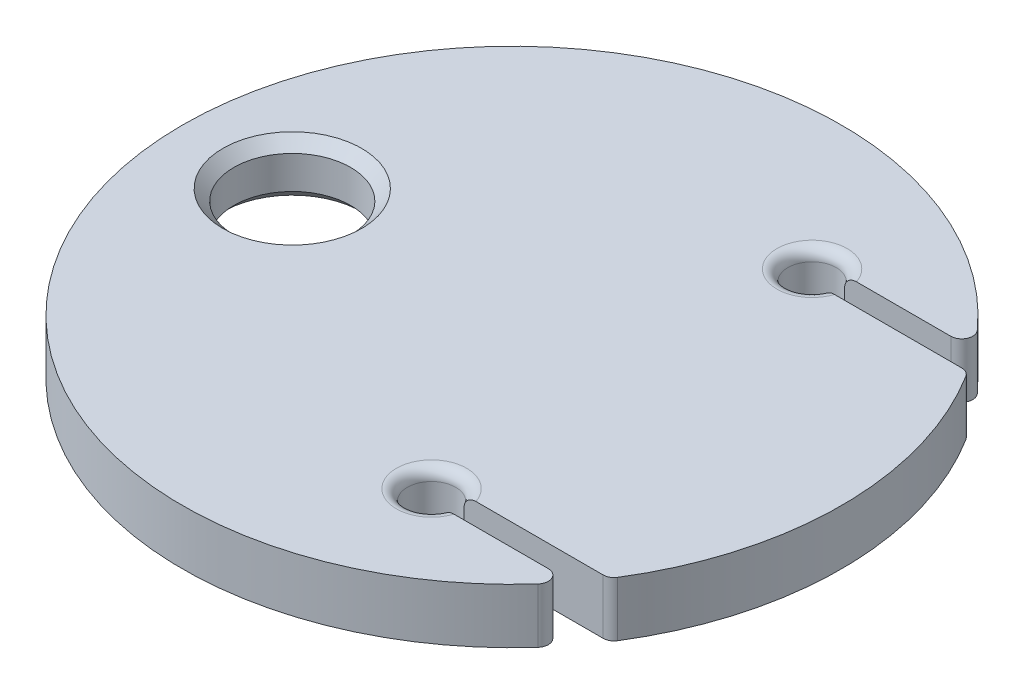
SolidWorks part; units mm, degrees
ref_plane "Front Plane" through (0, 0, 0) normal (0, 0, 1) x (1, 0, 0)
ref_plane "Top Plane" through (0, 0, 0) normal (0, 1, 0) x (1, 0, 0)
ref_plane "Right Plane" through (0, 0, 0) normal (1, 0, 0) x (0, 0, -1)
sketch "Sketch1" plane through (0, 0, 0) normal (0, 1, 0) x (1, 0, 0)
  circle A0 centre (0, 0) radius 19.05
  dimension "D1" = 38.1
extrude "Boss-Extrude1" add sketch "Sketch1" along normal blind 3.175
sketch "Sketch2" plane through (0, 3.175, 0) normal (0, 1, 0) x (1, 0, 0)
  line L0 (6.35, -10.9985) -> (6.35, 10.9985) construction
  line L1 (6.35, 10.9985) -> (-6.35, 10.9985) construction
  line L2 (6.35, -10.9985) -> (-6.35, -10.9985) construction
  line L3 (10.0041, -7.8235) -> (-10.0041, -7.8235) construction
  line L4 (10.0041, 7.8235) -> (-10.0041, 7.8235) construction
  line L5 (10.0041, -7.8235) -> (10.0041, 7.8235) construction
  circle A0 centre (0, 0) radius 12.7 construction
  point P6 (6.35, 0)
  dimension "D1" = 25.4
  dimension "D2" = 6.35
  dimension "D3" = 3.175
hole_wizard "Tiedown Hole" positions "Sketch3" profile "Sketch4" hole size "1/4" standard "ANSI Inch" end condition through all
sketch "Sketch3" plane through (0, 3.175, 0) normal (0, 1, 0) x (1, 0, 0)
  circle A0 centre (0, 0) radius 12.7 construction
  circle A1 centre (0, 0) radius 12.7 construction
  point P4 (-12.7, 0)
sketch "Sketch4" plane through (-12.7, 3.175, 0) normal (1, 0, 0) x (0, 0, 1)
  line L0 (0, 0) -> (0, 3.175)
  line L1 (0, 3.175) -> (3.3782, 3.175)
  line L2 (3.3782, 3.175) -> (3.3782, 0)
  line L5 (3.3782, 0) -> (0, 0)
  line L11 (0, -6.35) -> (0, 107.95) construction
  dimension "Thru Hole Dia." = 6.7564
  dimension "Thru Hole Depth" = 3.175
sketch3d "3DSketch1"
  line L0 (6.35, 3.175, 10.9985) -> (6.35, 3.175, 22.6356) construction
  line L1 (6.35, 3.175, 10.9985) -> (6.35, 3.175, -10.9985) construction
  line L2 (6.35, 3.175, -10.9985) -> (6.35, 3.175, -21.5348) construction
  line L3 (6.35, 3.175, -7.8235) -> (6.35, 3.175, -19.0222) construction
  line L4 (6.35, 3.175, 7.8235) -> (6.35, 3.175, 19.2587) construction
  dimension "D1" = 180
  dimension "D2" = 180
  dimension "D3" = 3.175
  dimension "D4" = 3.175
ref_plane "Plane1" through (0, 3.175, 0) normal (0, 1, 0) x (1, 0, 0)
ref_plane "Plane2" through (0, 3.175, 0) normal (0, -1, 0) x (-1, 0, 0)
hole_wizard "Monofilament Hole" positions "Sketch6" profile "Sketch7" hole size "#35" standard "ANSI Inch" end condition through all
sketch "Sketch6" plane through (0, 3.175, 0) normal (0, -1, 0) x (-1, 0, 0)
  point P0 (-6.35, 10.9985)
sketch "Sketch7" plane through (6.35, 3.175, -10.9985) normal (1, 0, 0) x (0, 0, 1)
  line L0 (0, 0) -> (0, 3.175)
  line L1 (0, 3.175) -> (1.397, 3.175)
  line L2 (1.397, 3.175) -> (1.397, 0)
  line L5 (1.397, 0) -> (0, 0)
  line L11 (0, -6.35) -> (0, 107.95) construction
  dimension "Thru Hole Dia." = 2.794
  dimension "Thru Hole Depth" = 3.175
hole_wizard "Monofilament Hole 2" positions "Sketch8" profile "Sketch9" hole size "#35" standard "ANSI Inch" end condition through all
sketch "Sketch8" plane through (0, 3.175, 0) normal (0, 1, 0) x (1, 0, 0)
  point P3 (6.35, -10.9985)
sketch "Sketch9" plane through (6.35, 3.175, 10.9985) normal (1, 0, 0) x (0, 0, 1)
  line L0 (0, 0) -> (0, 3.175)
  line L1 (0, 3.175) -> (1.397, 3.175)
  line L2 (1.397, 3.175) -> (1.397, 0)
  line L5 (1.397, 0) -> (0, 0)
  line L11 (0, -6.35) -> (0, 107.95) construction
  dimension "Thru Hole Dia." = 2.794
  dimension "Thru Hole Depth" = 3.175
chamfer "Chamfer1" distance 0.635 angle 45 2 edges at (-12.7, 0, 3.3782) (-12.7, 3.175, 3.3782)
ref_plane "Plane4" through (6.35, 0, 0) normal (1, 0, 0) x (0, 0, -1)
sketch "Sketch10" plane through (6.35, 6.35, 0) normal (1, 0, 0) x (0, 0, 1)
  line L0 (10.9985, 3.175) -> (22.6356, 3.175) construction
  line L2 (11.6335, -3.175) -> (10.3635, -3.175)
  line L3 (11.6335, -3.175) -> (11.6335, 9.525)
  line L4 (11.6335, 9.525) -> (10.3635, 9.525)
  line L5 (10.3635, -3.175) -> (10.3635, 9.525)
  line L6 (11.6335, -3.175) -> (10.3635, 9.525) construction
  line L7 (11.6335, 9.525) -> (10.3635, -3.175) construction
  line L9 (-11.6335, 9.525) -> (-10.3635, 9.525)
  line L10 (-11.6335, 9.525) -> (-11.6335, -3.175)
  line L11 (-11.6335, -3.175) -> (-10.3635, -3.175)
  line L12 (-10.3635, 9.525) -> (-10.3635, -3.175)
  line L13 (-11.6335, 9.525) -> (-10.3635, -3.175) construction
  line L14 (-11.6335, -3.175) -> (-10.3635, 9.525) construction
  line L15 (-10.9985, 3.175) -> (-21.5348, 3.175) construction
  point P3 (10.9985, 3.175)
  point P9 (-10.9985, 3.175)
  dimension "D1" = 1.27
  dimension "D2" = 12.7
extrude "Cut-Extrude1" cut sketch "Sketch10" along normal through all
fillet "Fillet1" radius 0.635 8 edges at (15.0852, 1.5875, -11.6335) (15.9844, 1.5875, -10.3635) (15.9844, 1.5875, 10.3635) (15.0852, 1.5875, 11.6335) (4.953, 0, -10.9985) (4.953, 0, 10.9985) (4.953, 3.175, -10.9985) (4.953, 3.175, 10.9985)
